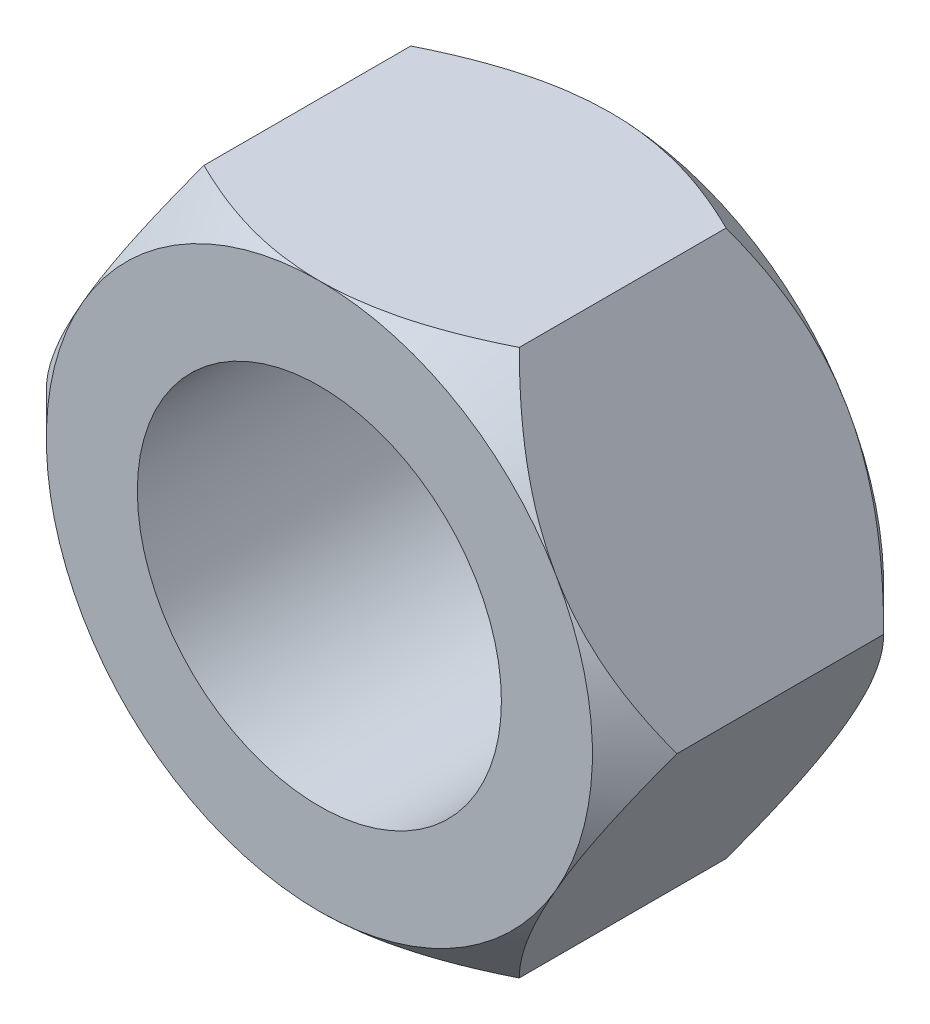
SolidWorks part; units mm, degrees
ref_plane "Front Plane" through (0, 0, 0) normal (0, 0, 1) x (1, 0, 0)
ref_plane "Top Plane" through (0, 0, 0) normal (0, 1, 0) x (1, 0, 0)
ref_plane "Right Plane" through (0, 0, 0) normal (1, 0, 0) x (0, 0, -1)
sketch "Sketch1" plane through (0, 0, 0) normal (0, 0, 1) x (1, 0, 0)
  line L1 (-8.6603, 15) -> (-17.3205, 0)
  line L2 (-17.3205, 0) -> (-8.6603, -15)
  line L3 (-8.6603, -15) -> (8.6603, -15)
  line L4 (8.6603, -15) -> (17.3205, 0)
  line L5 (17.3205, 0) -> (8.6603, 15)
  line L6 (8.6603, 15) -> (-8.6603, 15)
  circle A0 centre (0, 0) radius 15 construction
  dimension "D1" = 30
extrude "Boss-Extrude1" add sketch "Sketch1" along normal mid plane 16
sketch "Sketch2" plane through (0, 0, 8) normal (0, 0, 1) x (1, 0, 0)
  line L0 (-8.6603, 15) -> (-17.3205, 0) construction
  circle A0 centre (0, 0) radius 15
extrude "Cut-Extrude1" cut sketch "Sketch2" against normal through all draft 45 flip side to cut
mirror "Mirror1" about plane through (0, 0, 0) normal (0, 0, 1) of "Cut-Extrude1"
sketch "Sketch3" plane through (0, 0, -8) normal (0, 0, -1) x (-1, 0, 0)
  circle A0 centre (0, 0) radius 10
  dimension "D1" = 20
extrude "Cut-Extrude2" cut sketch "Sketch3" against normal through all
cosmetic thread "Cosmetic Thread1" parameters "D2"=24
